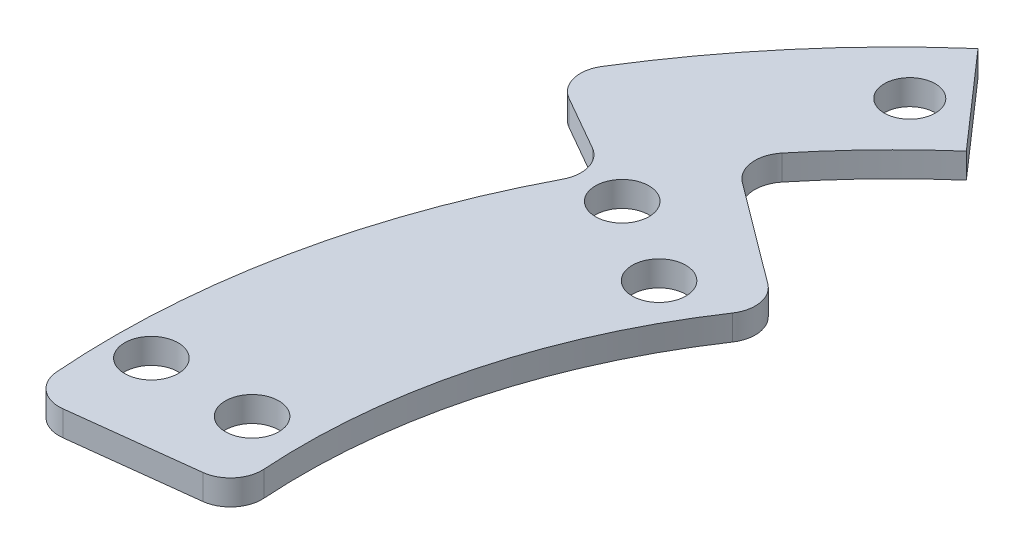
SolidWorks part; units mm, degrees
ref_plane "Front Plane" through (0, 0, 0) normal (0, 0, 1) x (1, 0, 0)
ref_plane "Top Plane" through (0, 0, 0) normal (0, 1, 0) x (1, 0, 0)
ref_plane "Right Plane" through (0, 0, 0) normal (1, 0, 0) x (0, 0, -1)
sketch "Sketch1" plane through (0, 0, 0) normal (0, 1, 0) x (1, 0, 0)
  line L0 (0, 0) -> (-59, 0) construction
  line L1 (0, 0) -> (-51.0955, 29.5) construction
  line L2 (-37.6558, 28.1254) -> (-49.6736, 37.1016)
  line L3 (-46.6736, -5.5294) -> (-61.5694, -7.2941)
  circle A0 centre (0, 0) radius 51 construction
  circle A1 centre (0, 0) radius 59 construction
  circle A2 centre (-44.1673, 25.5) radius 2.125
  circle A3 centre (-51.0955, 29.5) radius 2.125
  circle A4 centre (-59, 0) radius 2.125
  circle A5 centre (-51, 0) radius 2.125
  arc A6 (-37.6558, 28.1254) -> (-46.6736, -5.5294) centre (0, 0) ccw
  arc A7 (-49.6736, 37.1016) -> (-61.5694, -7.2941) centre (0, 0) ccw
  point P5 (-44.1673, 25.5)
  point P7 (-51, 0)
  dimension "D1" = 102
  dimension "D2" = 118
  dimension "D4" = 4.25
  dimension "D5" = 47
  dimension "D8" = 6
  dimension "D3" = 30
  dimension "D6" = 15
  dimension "D7" = 6
extrude "Boss-Extrude1" add sketch "Sketch1" along normal blind 2
sketch "Sketch3" plane through (0, 0, 0) normal (0, 1, 0) x (1, 0, 0)
  line L1 (-62.5064, 35.7345) -> (-53.8249, 30.7714)
  line L2 (0, 0) -> (-57.6855, 43.0857) construction
  line L3 (-57.6855, 43.0857) -> (-49.6736, 37.1016)
  line L5 (-37.6558, 28.1254) -> (-49.6736, 37.1016) construction
  arc A2 (-49.6736, 37.1016) -> (-61.5694, -7.2941) centre (0, 0) ccw construction
  arc A3 (-62.5064, 35.7345) -> (-57.6855, 43.0857) centre (0, 0) cw
  arc A4 (-53.8249, 30.7714) -> (-49.6736, 37.1016) centre (0, 0) cw
  dimension "D1" = 7
  dimension "D2" = 10
extrude "Boss-Extrude3" add sketch "Sketch3" along normal up to surface (2 mm away) up to face at (-44.1673, 2, -23.375)
sketch "Sketch5" plane through (0, 0, 0) normal (0, 1, 0) x (1, 0, 0)
  line L0 (-37.6558, 28.1254) -> (-57.6855, 43.0857) construction
  line L1 (-47.4669, 54.1377) -> (-40.8743, 46.6186)
  line L2 (-57.6855, 43.0857) -> (-49.6736, 37.1016)
  arc A0 (-57.6855, 43.0857) -> (-47.4669, 54.1377) centre (0, 0) cw
  arc A1 (-40.8743, 46.6186) -> (-49.6736, 37.1016) centre (0, 0) ccw
  arc A2 (-53.8249, 30.7714) -> (-61.5694, -7.2941) centre (0, 0) ccw construction
  dimension "D1" = 12
extrude "Boss-Extrude4" add sketch "Sketch5" along normal up to surface (2 mm away) up to face at (-44.1673, 2, -23.375)
fillet "Fillet1" radius 2.5 6 edges at (-46.6736, 1, 5.5294) (-61.5694, 1, 7.2941) (-62.5064, 1, -35.7345) (-53.8249, 1, -30.7714) (-37.6558, 1, -28.1254) (-49.6736, 1, -37.1016)
sketch "Sketch6" plane through (0, 2, 0) normal (0, 1, 0) x (1, 0, 0)
  line L0 (0, 0) -> (-50.2352, 51.5793) construction
  line L1 (-40.8743, 46.6186) -> (-47.4669, 54.1377) construction
  arc A0 (-47.4669, 54.1377) -> (-61.1805, 37.9598) centre (0, 0) ccw construction
  circle A1 centre (-46.7467, 47.9974) radius 2.025
  dimension "D1" = 4.05
  dimension "D2" = 67
  dimension "D3" = 3
extrude "Cut-Extrude1" cut sketch "Sketch6" against normal through all both and the other way through all
